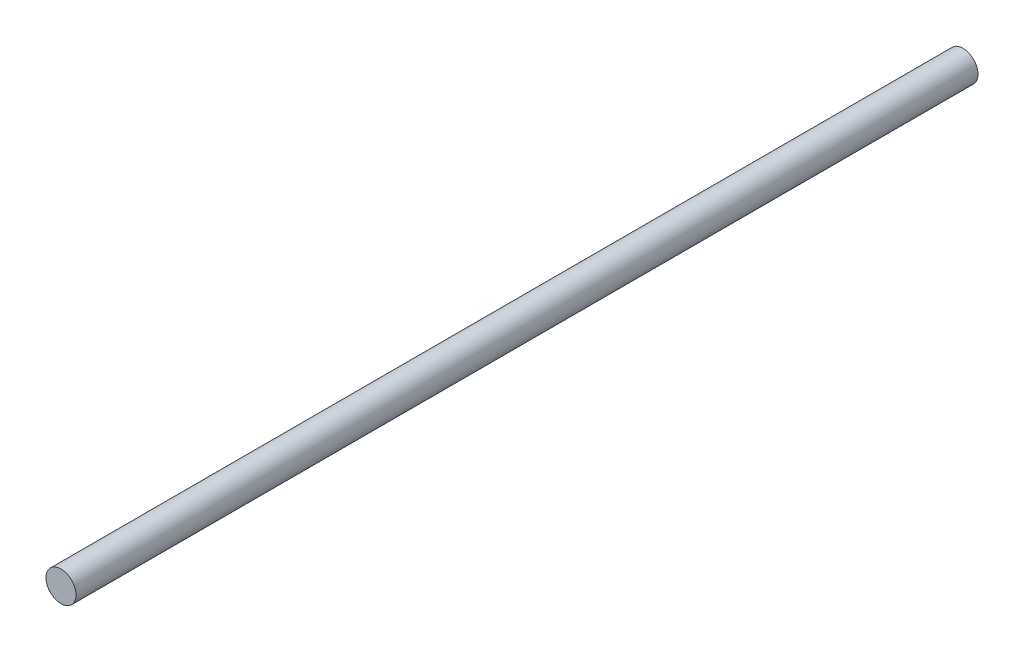
SolidWorks part; units mm, degrees
ref_plane "Front Plane" through (0, 0, 0) normal (0, 0, 1) x (1, 0, 0)
ref_plane "Top Plane" through (0, 0, 0) normal (0, 1, 0) x (1, 0, 0)
ref_plane "Right Plane" through (0, 0, 0) normal (1, 0, 0) x (0, 0, -1)
sketch "Sketch1" plane through (0, 0, 0) normal (0, 0, 1) x (1, 0, 0)
  circle A0 centre (0, 0) radius 0.3
extrude "Boss-Extrude1" add sketch "Sketch1" along normal blind 18
